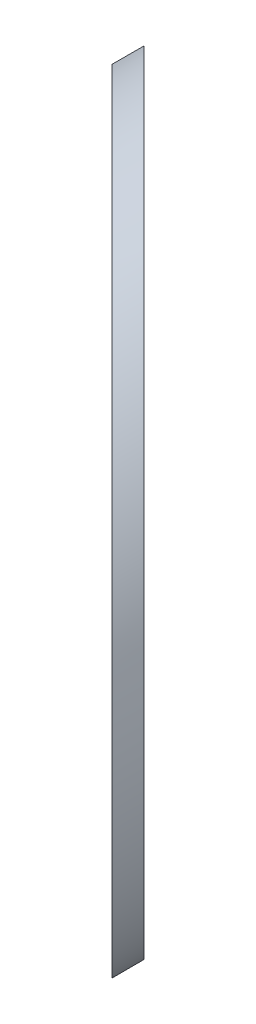
SolidWorks part; units mm, degrees
ref_plane "前视基准面" through (0, 0, 0) normal (0, 0, 1) x (1, 0, 0)
ref_plane "上视基准面" through (0, 0, 0) normal (0, 1, 0) x (1, 0, 0)
ref_plane "右视基准面" through (0, 0, 0) normal (1, 0, 0) x (0, 0, -1)
sketch "草图1" plane through (0, 0, 0) normal (0, 0, 1) x (1, 0, 0)
  circle A0 centre (0, 0) radius 12.5
  dimension "D1" = 25
extrude "凸台-拉伸1" add sketch "草图1" along normal blind 61
sketch "草图2" plane through (0, 0, 0) normal (0, 1, 0) x (1, 0, 0)
  line L0 (-39.3783, 21.3445) -> (32.9463, -50.9802)
  line L1 (-40.0854, 20.6374) -> (32.2392, -51.6873)
  line L2 (-40.0854, 20.6374) -> (-29.5005, -63.952)
  line L3 (-29.5005, -63.952) -> (29.8587, -63.952)
  line L4 (32.2392, -51.6873) -> (29.8587, -63.952)
  line L5 (32.9463, -50.9802) -> (32.9463, 3.7053)
  line L6 (32.9463, 3.7053) -> (-39.3783, 21.3445)
  line L7 (0, 0) -> (0, -25.8513) construction
  dimension "D2" = 135
  dimension "D1" = 1
extrude "切除-拉伸1" cut sketch "草图2" against normal mid plane 61
sketch "草图3" plane through (-9.0169, 0, 9.0169) normal (0.7071, 0, -0.7071) x (-0.7071, 0, -0.7071)
  line L0 (-30.4295, 0) -> (4.9258, 0) construction
  line L1 (-12.7519, 12.5) -> (-12.7519, -12.5) construction
  ellipse E0 centre (-12.7519, 0) end of major axis (4.9258, 0) minor radius 12.5 construction
